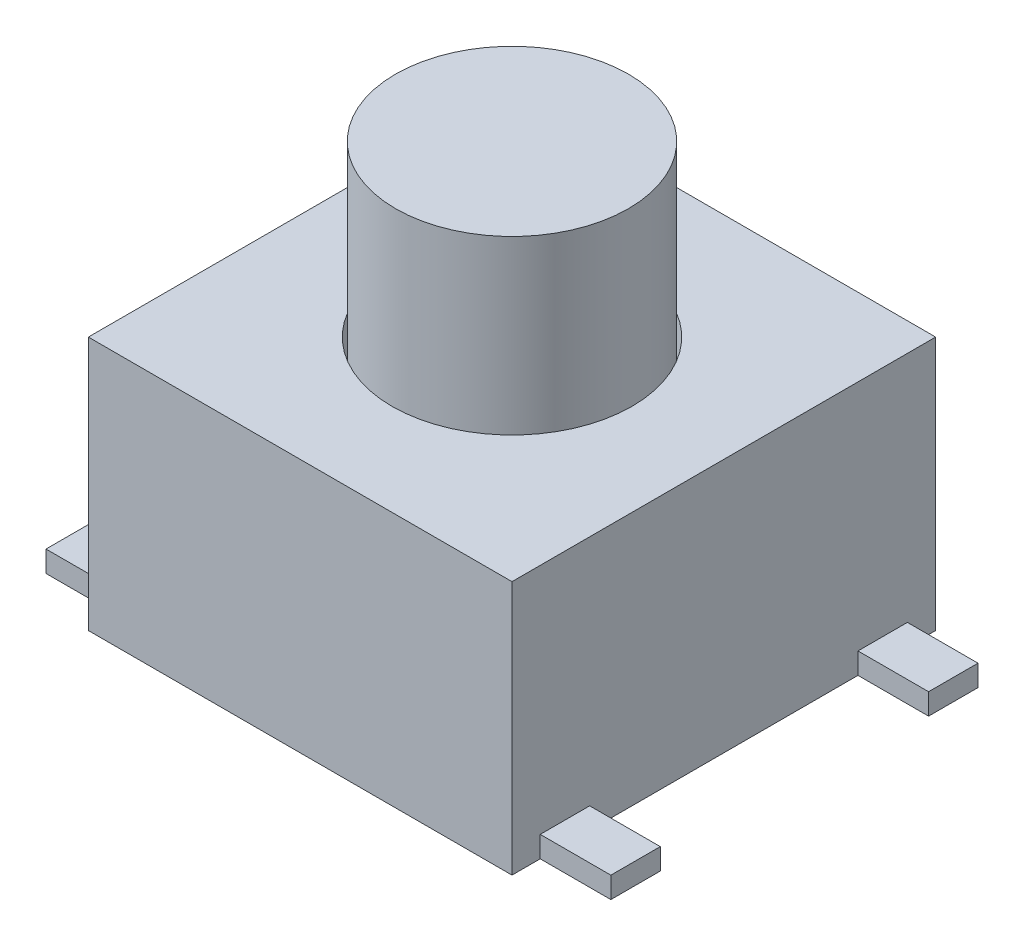
SolidWorks part; units mm, degrees
ref_plane "前视基准面" through (0, 0, 0) normal (0, 0, 1) x (1, 0, 0)
ref_plane "上视基准面" through (0, 0, 0) normal (0, 1, 0) x (1, 0, 0)
ref_plane "右视基准面" through (0, 0, 0) normal (1, 0, 0) x (0, 0, -1)
sketch "草图1" plane through (0, 0, 0) normal (0, 1, 0) x (1, 0, 0)
  line L1 (-3, 3) -> (3, 3)
  line L2 (-3, 3) -> (-3, -3)
  line L3 (-3, -3) -> (3, -3)
  line L4 (3, 3) -> (3, -3)
  line L5 (-3, 3) -> (3, -3) construction
  line L6 (-3, -3) -> (3, 3) construction
  point P0 (0, 0)
  dimension "D1" = 6
extrude "凸台-拉伸1" add sketch "草图1" along normal blind 3.6
sketch "草图2" plane through (-3, 0, 0) normal (-1, 0, 0) x (0, 0, 1)
  line L0 (-3, 0) -> (3, 0) construction
  line L1 (-2.6, 0) -> (-1.9, 0)
  line L2 (-2.6, 0) -> (-2.6, 0.3)
  line L3 (-2.6, 0.3) -> (-1.9, 0.3)
  line L4 (-1.9, 0) -> (-1.9, 0.3)
  line L5 (1.9, 0) -> (1.9, 0.3)
  line L6 (1.9, 0) -> (2.6, 0)
  line L7 (2.6, 0) -> (2.6, 0.3)
  line L8 (1.9, 0.3) -> (2.6, 0.3)
  line L10 (-1.9, 0) -> (1.9, 0) construction
  point P7 (0, 0)
  dimension "D1" = 0.7
  dimension "D2" = 0.3
  dimension "D3" = 4.5
  dimension "D4" = 2
extrude "凸台-拉伸2" add sketch "草图2" along normal blind 1
mirror "镜向1" about plane through (0, 0, 0) normal (1, 0, 0) of "凸台-拉伸2"
sketch "草图3" plane through (0, 3.6, 0) normal (0, 1, 0) x (1, 0, 0)
  circle A0 centre (0, 0) radius 1.7
  dimension "D1" = 3.4
extrude "切除-拉伸1" cut sketch "草图3" against normal offset from surface (2.6 mm away) 1 up to face at (0, 0, 0)
sketch "草图4" plane through (0, 1, 0) normal (0, 1, 0) x (1, 0, 0)
  circle A0 centre (0, 0) radius 1.65
  dimension "D1" = 3.3
extrude "凸台-拉伸3" add sketch "草图4" along normal offset from surface (5 mm away) 6 separate body up to face at (0, 0, 0)
